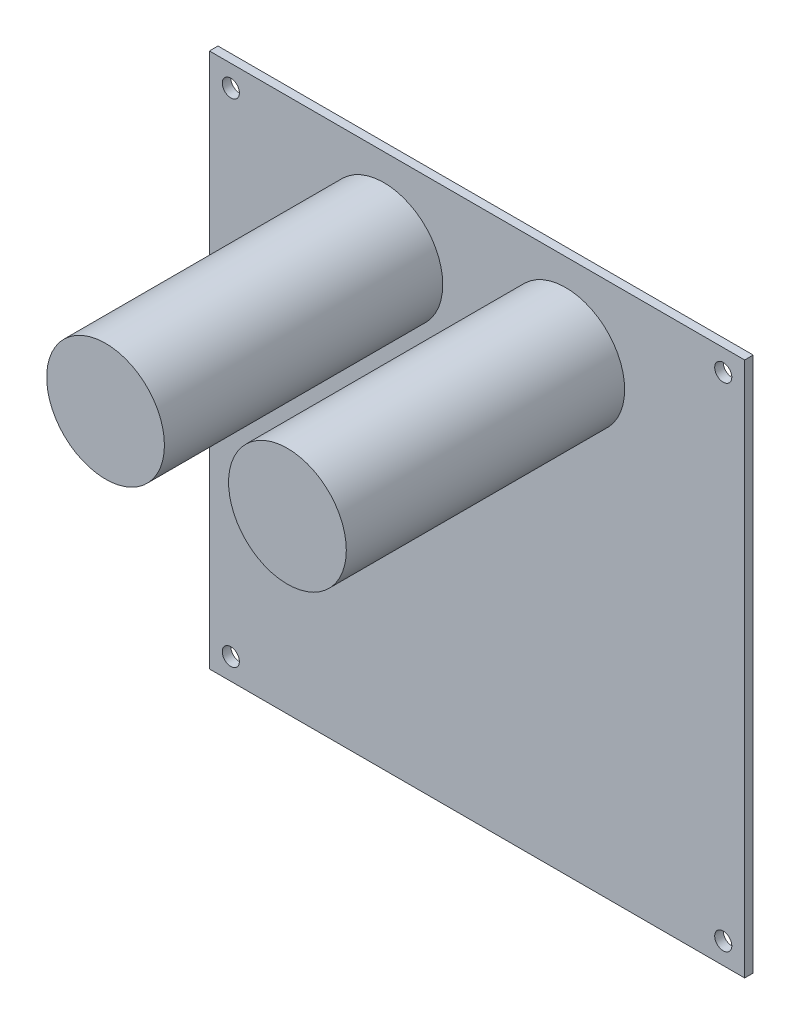
SolidWorks part; units mm, degrees
ref_plane "Plan de face" through (0, 0, 0) normal (0, 0, 1) x (1, 0, 0)
ref_plane "Plan de dessus" through (0, 0, 0) normal (0, 1, 0) x (1, 0, 0)
ref_plane "Plan de droite" through (0, 0, 0) normal (1, 0, 0) x (0, 0, -1)
sketch "Esquisse1" plane through (0, 0, 0) normal (0, 0, 1) x (1, 0, 0)
  line L0 (-46, 46) -> (46, -46) construction
  line L1 (-50, 50) -> (50, 50)
  line L2 (-50, 50) -> (-50, -50)
  line L3 (-50, -50) -> (50, -50)
  line L4 (50, 50) -> (50, -50)
  circle A0 centre (-46, 46) radius 1.6
  circle A1 centre (46, 46) radius 1.6
  circle A2 centre (-46, -46) radius 1.6
  circle A3 centre (46, -46) radius 1.6
  point P4 (0, 50)
  point P6 (-50, 0)
  point P15 (0, 0)
  point P16 (0, 0)
  point P17 (0, 0)
  point P18 (0, 0)
  point P19 (0, 0)
  dimension "D3" = 3.2
  dimension "D1" = 100
  dimension "D2" = 100
  dimension "D4" = 92
  dimension "D5" = 92
extrude "Boss.-Extru.1" add sketch "Esquisse1" along normal blind 1.6
sketch "Esquisse2" plane through (0, 0, 1.6) normal (0, 0, 1) x (1, 0, 0)
  line L0 (50, 50) -> (-50, 50) construction
  circle A0 centre (-17.4051, 34) radius 11
  circle A1 centre (16.5774, 34) radius 11
  point P4 (0, 0)
  point P5 (-13.7447, 35.1455)
  point P8 (16.5774, 34)
  point P9 (-17.4051, 34)
  dimension "D1" = 22
  dimension "D2" = 16
extrude "Boss.-Extru.2" add sketch "Esquisse2" along normal blind 52
